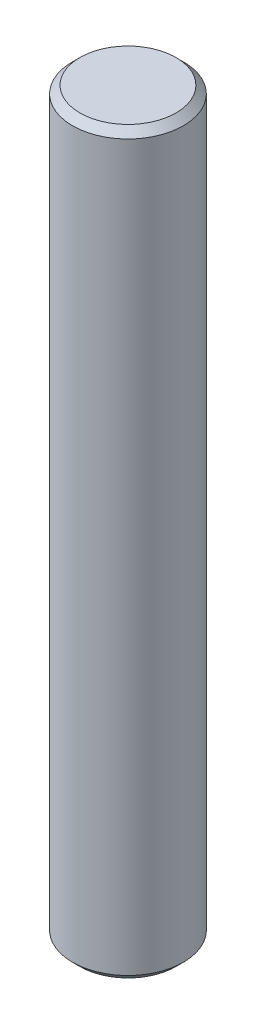
SolidWorks part; units mm, degrees
ref_plane "Plan de face" through (0, 0, 0) normal (0, 0, 1) x (1, 0, 0)
ref_plane "Plan de dessus" through (0, 0, 0) normal (0, 1, 0) x (1, 0, 0)
ref_plane "Plan de droite" through (0, 0, 0) normal (1, 0, 0) x (0, 0, -1)
sketch "Esquisse1" plane through (0, 0, 0) normal (0, 1, 0) x (1, 0, 0)
  circle A0 centre (0, 0) radius 1.5
extrude "Extrusion1" add sketch "Esquisse1" along normal blind 20
chamfer "Chanfrein1" distance 0.2 angle 45 2 edges at (0, 0, 1.5) (0, 20, 1.5)
